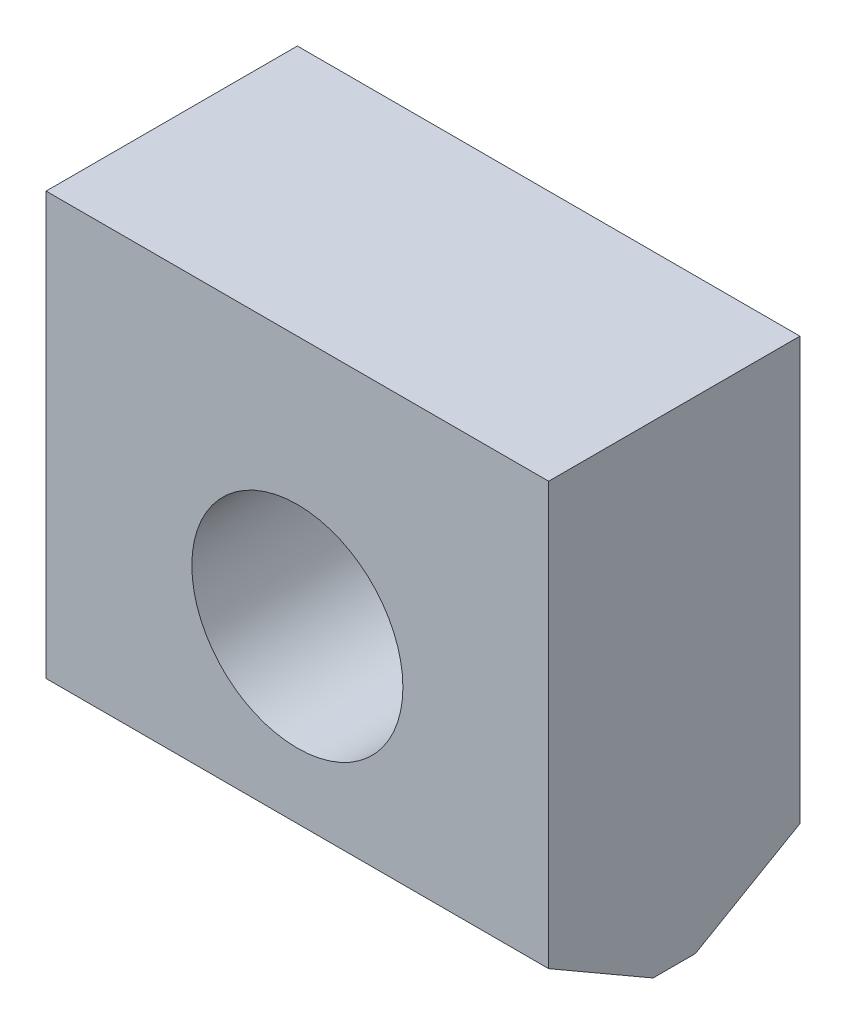
SolidWorks part; units mm, degrees
material "Простая углеродистая сталь"
ref_plane "Спереди" through (0, 0, 0) normal (0, 0, 1) x (1, 0, 0)
ref_plane "Сверху" through (0, 0, 0) normal (0, 1, 0) x (1, 0, 0)
ref_plane "Справа" through (0, 0, 0) normal (1, 0, 0) x (0, 0, -1)
sketch "Эскиз1" plane through (0, 0, 0) normal (0, 0, 1) x (1, 0, 0)
  line L1 (0, 0) -> (50, 0)
  line L2 (0, 0) -> (0, 48)
  line L3 (0, 48) -> (50, 48)
  line L4 (50, 0) -> (50, 48)
  point P5 (25, 48)
  dimension "D1" = 48
  dimension "D2" = 50
extrude "Бобышка-Вытянуть1" add sketch "Эскиз1" along normal blind 25
sketch "Эскиз2" plane through (0, 0, 25) normal (0, 0, 1) x (1, 0, 0)
  line L0 (0, 0) -> (50, 0) construction
  line L1 (50, 0) -> (50, 48) construction
  circle A0 centre (25, 23) radius 10.5
  dimension "D2" = 23
  dimension "D3" = 25
  dimension "D4" = 21
extrude "Вырез-Вытянуть1" cut sketch "Эскиз2" against normal through all
chamfer "Фаска1" distance 6 angle 60 1 edges at (25, 0, 0)
chamfer "Фаска2" distance 6 angle 60 1 edges at (25, 0, 25)
